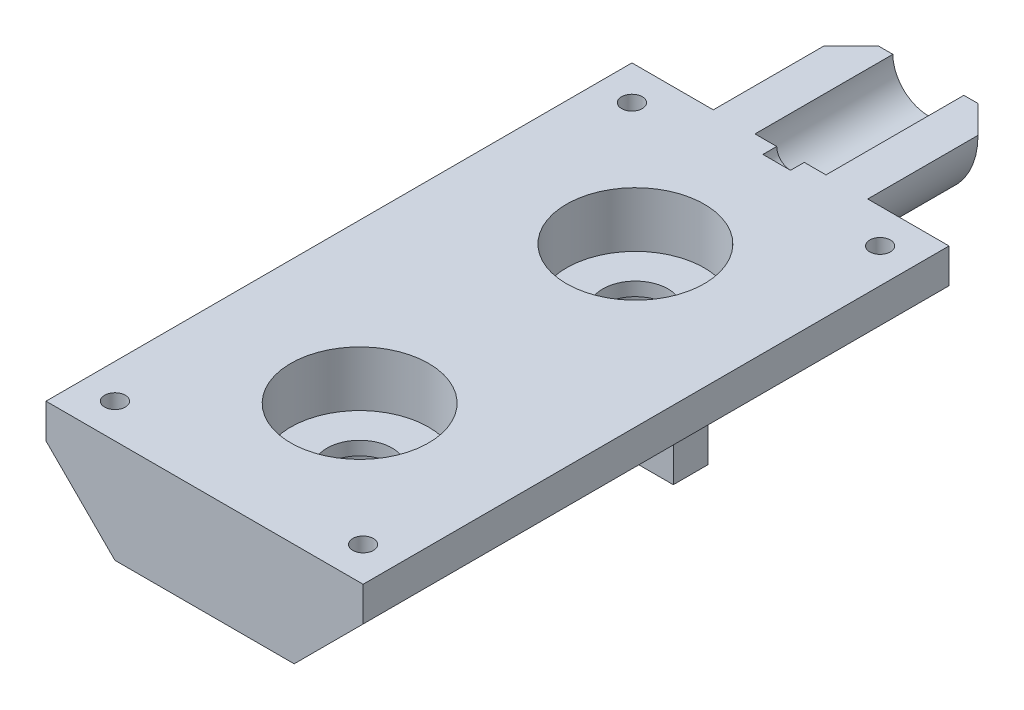
SolidWorks part; units mm, degrees
ref_plane "Front Plane" through (0, 0, 0) normal (0, 0, 1) x (1, 0, 0)
ref_plane "Top Plane" through (0, 0, 0) normal (0, 1, 0) x (1, 0, 0)
ref_plane "Right Plane" through (0, 0, 0) normal (1, 0, 0) x (0, 0, -1)
sketch "Sketch1" plane through (0, 0, 0) normal (0, 1, 0) x (1, 0, 0)
  line L1 (-29.21, 53.975) -> (29.21, 53.975)
  line L2 (-29.21, 53.975) -> (-29.21, -53.975)
  line L3 (-29.21, -53.975) -> (29.21, -53.975)
  line L4 (29.21, 53.975) -> (29.21, -53.975)
  line L5 (-29.21, 53.975) -> (29.21, -53.975) construction
  line L6 (-29.21, -53.975) -> (29.21, 53.975) construction
  point P0 (0, 0)
  dimension "D1" = 58.42
  dimension "D2" = 107.95
extrude "Boss-Extrude1" add sketch "Sketch1" along normal blind 38.1
chamfer "Chamfer1" distance 12.7 angle 45 1 edges at (-29.21, 38.1, 0)
chamfer "Chamfer2" distance 12.7 angle 45 3 edges at (29.21, 0, 0) (29.21, 38.1, 0) (-29.21, 0, 0)
sketch "Sketch2" plane through (0, 0, -53.975) normal (0, 0, -1) x (-1, 0, 0)
  line L0 (-29.21, 25.4) -> (-29.21, 12.7) construction
  circle A0 centre (0, 19.05) radius 6.5405
  circle A1 centre (0, 19.05) radius 14.224
  point P2 (-29.21, 19.05)
  dimension "D1" = 13.081
  dimension "D2" = 28.448
extrude "Boss-Extrude2" add sketch "Sketch2" along normal blind 25.4
chamfer "Chamfer3" distance 5.08 angle 45 1 edges at (-14.224, 19.05, -79.375)
sketch "Sketch3" plane through (0, 0, 53.975) normal (0, 0, 1) x (1, 0, 0)
  line L0 (-29.21, 19.05) -> (29.21, 19.05)
  line L1 (-29.21, 25.4) -> (-29.21, 12.7) construction
  line L2 (29.21, 25.4) -> (29.21, 12.7) construction
  line L3 (29.21, 19.05) -> (29.21, 41.1741)
  line L4 (29.21, 41.1741) -> (-29.21, 41.1741)
  line L5 (-29.21, 41.1741) -> (-29.21, 19.05)
extrude "Cut-Extrude1" cut sketch "Sketch3" against normal blind 152.4
sketch "Sketch4" plane through (0, 0, 0) normal (0, -1, 0) x (-1, 0, 0)
  circle A0 centre (0, 25.4) radius 8.85
  dimension "D1" = 17.7
  dimension "D2" = 25.4
extrude "Cut-Extrude2" cut sketch "Sketch4" against normal blind 6.4
sketch "Sketch5" plane through (0, 6.4, 0) normal (0, -1, 0) x (1, 0, 0)
  circle A0 centre (0, -25.4) radius 6
  dimension "D1" = 12
extrude "Cut-Extrude3" cut sketch "Sketch5" against normal blind 17.16
sketch "Sketch6" plane through (0, 19.05, 0) normal (0, 1, 0) x (1, 0, 0)
  circle A0 centre (0, 25.4) radius 12.7
  dimension "D1" = 25.4
extrude "Cut-Extrude4" cut sketch "Sketch6" against normal blind 10.16
mirror "Mirror1" about plane through (0, 0, 0) normal (0, 0, 1) of "Cut-Extrude4", "Cut-Extrude3", "Cut-Extrude2", "Cut-Extrude1"
sketch "Sketch7" plane through (0, 0, -53.975) normal (0, 0, -1) x (-1, 0, 0)
  line L0 (6.5405, 19.05) -> (-6.5405, 19.05) construction
  circle A0 centre (0, 19.05) radius 2.54
  dimension "D1" = 5.08
extrude "Cut-Extrude5" cut sketch "Sketch7" against normal blind 2.54
sketch "Sketch9" plane through (0, 0, 0) normal (0, -1, 0) x (-1, 0, 0)
  circle A0 centre (0, 44.45) radius 1.27
  circle A1 centre (0, -50.8) radius 1.27
  dimension "D1" = 2.54
  dimension "D2" = 2.54
  dimension "D3" = 44.45
  dimension "D4" = 50.8
extrude "Cut-Extrude7" cut sketch "Sketch9" against normal blind 5.08
sketch "Sketch10" plane through (0, 0, 0) normal (0, -1, 0) x (-1, 0, 0)
  line L1 (-16.51, 9.525) -> (-22.86, 9.525)
  line L2 (-16.51, 9.525) -> (-16.51, 15.875)
  line L3 (-16.51, 15.875) -> (-22.86, 15.875)
  line L4 (-22.86, 9.525) -> (-22.86, 15.875)
  circle A0 centre (-19.685, 12.7) radius 1.27
  point P8 (-22.86, 12.7)
  point P9 (-19.685, 9.525)
  dimension "D1" = 2.54
  dimension "D2" = 6.35
  dimension "D3" = 6.35
  dimension "D4" = 9.525
extrude "Boss-Extrude3" add sketch "Sketch10" against normal blind 7.62
sketch "Sketch11" plane through (0, 0, 0) normal (0, -1, 0) x (-1, 0, 0)
  circle A0 centre (-19.685, 12.7) radius 1.27
extrude "Cut-Extrude8" cut sketch "Sketch11" against normal blind 5.08
sketch "Sketch12" plane through (0, 0, 0) normal (0, -1, 0) x (-1, 0, 0)
  line L0 (16.51, -53.975) -> (16.51, 53.975) construction
  line L1 (16.51, -10.16) -> (26.67, -10.16)
  line L2 (16.51, -10.16) -> (16.51, -16.51)
  line L3 (16.51, -16.51) -> (26.67, -16.51)
  line L4 (26.67, -10.16) -> (26.67, -16.51)
  dimension "D1" = 6.35
  dimension "D2" = 10.16
  dimension "D3" = 10.16
extrude "Boss-Extrude4" add sketch "Sketch12" against normal blind 12.7 separate body
sketch "Sketch13" plane through (0, 0, 0) normal (0, -1, 0) x (-1, 0, 0)
  line L0 (26.67, -10.16) -> (16.51, -10.16) construction
  line L2 (26.67, -16.51) -> (26.67, -10.16) construction
  circle A0 centre (22.86, -13.335) radius 1.27
  dimension "D1" = 2.54
  dimension "D2" = 3.175
  dimension "D3" = 3.81
extrude "Cut-Extrude9" cut sketch "Sketch13" against normal blind 5.08
sketch "Sketch14" plane through (0, 19.05, 0) normal (0, 1, 0) x (1, 0, 0)
  line L0 (-29.21, 53.975) -> (-29.21, -53.975) construction
  line L2 (-29.21, 53.975) -> (-14.224, 53.975) construction
  line L3 (29.21, 53.975) -> (29.21, -53.975) construction
  circle A0 centre (22.86, 47.625) radius 1.905
  circle A1 centre (-22.86, 47.625) radius 1.905
  dimension "D2" = 6.35
  dimension "D3" = 3.81
  dimension "D4" = 6.35
  dimension "D1" = 6.35
extrude "Cut-Extrude10" cut sketch "Sketch14" against normal blind 40.64
mirror "Mirror2" about plane through (0, 0, 0) normal (0, 0, 1) of "Cut-Extrude10"
sketch "Sketch15" plane through (0, 0, 0) normal (0, -1, 0) x (-1, 0, 0)
  circle A0 centre (22.86, 47.625) radius 2.921
  circle A1 centre (-22.86, 47.625) radius 2.921
  circle A2 centre (-22.86, -47.625) radius 2.921
  circle A3 centre (22.86, -47.625) radius 2.921
  dimension "D1" = 5.842
  dimension "D2" = 5.842
  dimension "D3" = 5.842
  dimension "D4" = 5.842
extrude "Cut-Extrude11" cut sketch "Sketch15" against normal blind 15.24
